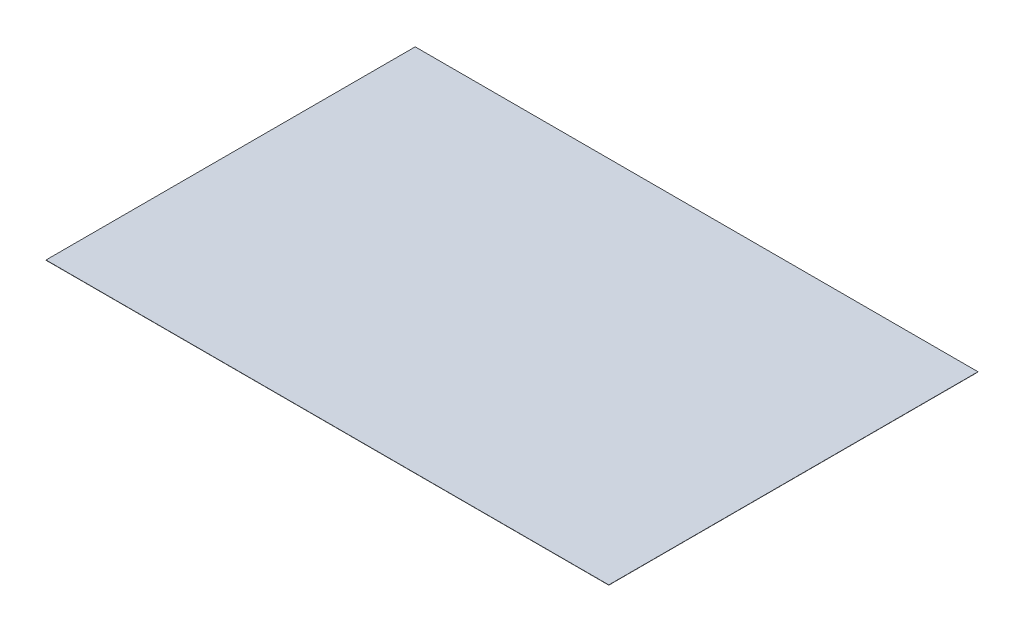
SolidWorks part; units mm, degrees
ref_plane "Plan de face" through (0, 0, 0) normal (0, 0, 1) x (1, 0, 0)
ref_plane "Plan de dessus" through (0, 0, 0) normal (0, 1, 0) x (1, 0, 0)
ref_plane "Plan de droite" through (0, 0, 0) normal (1, 0, 0) x (0, 0, -1)
sketch "Esquisse1" plane through (0, 0, 0) normal (0, 1, 0) x (1, 0, 0)
  line L1 (-250, -164) -> (250, -164)
  line L2 (-250, -164) -> (-250, 164)
  line L3 (-250, 164) -> (250, 164)
  line L4 (250, -164) -> (250, 164)
  line L5 (-250, -164) -> (250, 164) construction
  line L6 (-250, 164) -> (250, -164) construction
  point P0 (0, 0)
  dimension "D1" = 500
  dimension "D2" = 328
extrude "Boss.-Extru.1" add sketch "Esquisse1" along normal blind 0.2
